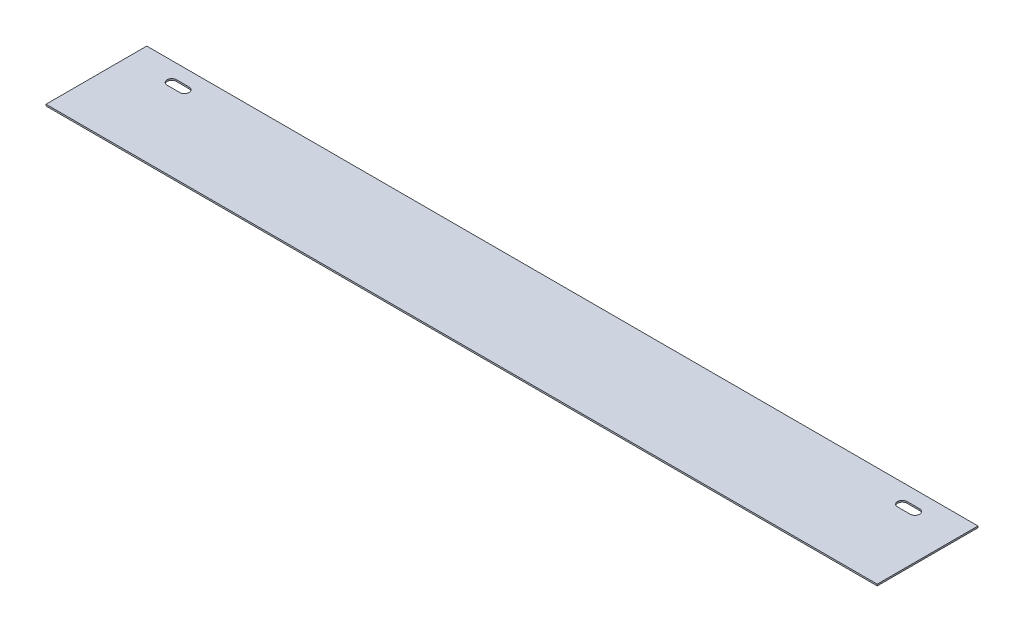
SolidWorks part; units mm, degrees
ref_plane "Front" through (0, 0, 0) normal (0, 0, 1) x (1, 0, 0)
ref_plane "Top" through (0, 0, 0) normal (0, 1, 0) x (1, 0, 0)
ref_plane "Right" through (0, 0, 0) normal (1, 0, 0) x (0, 0, -1)
sketch "Sketch1" plane through (0, 0, 0) normal (0, 1, 0) x (1, 0, 0)
  line L1 (0, 0) -> (838.2, 0)
  line L2 (0, 0) -> (0, -101.6)
  line L3 (0, -101.6) -> (838.2, -101.6)
  line L4 (838.2, 0) -> (838.2, -101.6)
  dimension "D1" = 101.6
  dimension "D2" = 838.2
extrude "Boss-Extrude1" add sketch "Sketch1" along normal blind 1.6002
sketch "Sketch2" plane through (0, 1.6002, 0) normal (0, 1, 0) x (1, 0, 0)
  line L0 (44.45, -19.177) -> (57.15, -19.177) construction
  line L1 (44.45, -14.4145) -> (57.15, -14.4145)
  line L2 (44.45, -23.9395) -> (57.15, -23.9395)
  line L3 (781.05, -19.177) -> (793.75, -19.177) construction
  line L4 (781.05, -14.4145) -> (793.75, -14.4145)
  line L5 (781.05, -23.9395) -> (793.75, -23.9395)
  line L6 (0, 0) -> (0, -101.6) construction
  line L7 (838.2, -101.6) -> (838.2, 0) construction
  line L8 (838.2, 0) -> (0, 0) construction
  arc A0 (44.45, -14.4145) -> (44.45, -23.9395) centre (44.45, -19.177) ccw
  arc A1 (57.15, -23.9395) -> (57.15, -14.4145) centre (57.15, -19.177) ccw
  arc A2 (781.05, -14.4145) -> (781.05, -23.9395) centre (781.05, -19.177) ccw
  arc A3 (793.75, -23.9395) -> (793.75, -14.4145) centre (793.75, -19.177) ccw
  point P2 (50.8, -19.177)
  point P7 (787.4, -19.177)
  dimension "D6" = 12.7
  dimension "D7" = 12.7
  dimension "D1" = 50.8
  dimension "D2" = 50.8
  dimension "D3" = 19.177
  dimension "D4" = 9.525
  dimension "D5" = 9.525
extrude "Cut-Extrude1" cut sketch "Sketch2" against normal through all
